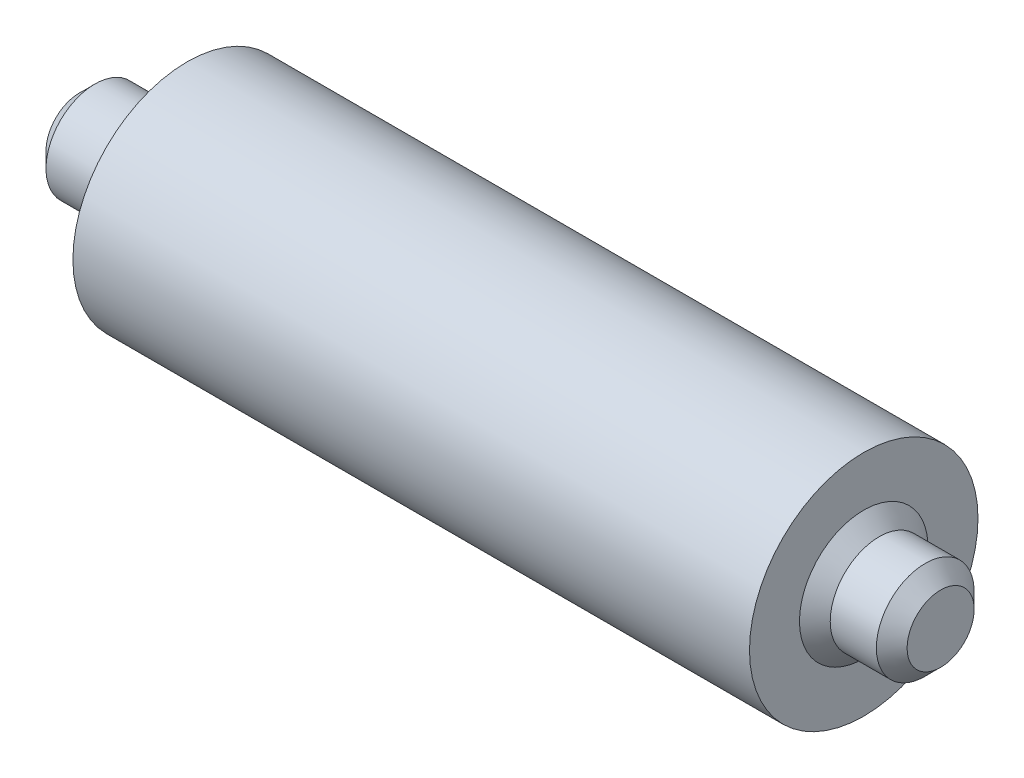
SolidWorks part; units mm, degrees
ref_plane "Front Plane" through (0, 0, 0) normal (0, 0, 1) x (1, 0, 0)
ref_plane "Top Plane" through (0, 0, 0) normal (0, 1, 0) x (1, 0, 0)
ref_plane "Right Plane" through (0, 0, 0) normal (1, 0, 0) x (0, 0, -1)
sketch "Sketch1" plane through (0, 0, 0) normal (0, 0, 1) x (1, 0, 0)
  line L0 (-28.1429, 0) -> (27.8571, 0) construction
  line L1 (-28.1429, 0) -> (-28.1429, 3.18)
  line L2 (-28.1429, 3.18) -> (-21.1429, 3.18)
  line L3 (-21.1429, 3.18) -> (-21.1429, 7.43)
  line L4 (-21.1429, 7.43) -> (22.8571, 7.43)
  line L5 (22.8571, 7.43) -> (22.8571, 3.18)
  line L6 (22.8571, 3.18) -> (27.8571, 3.18)
  line L7 (27.8571, 3.18) -> (27.8571, 0)
  line L8 (-28.1429, 0) -> (27.8571, 0)
  point P1 (-28.1429, 1.59)
  point P4 (-28.1429, 0)
  dimension "D1" = 56
  dimension "D2" = 44
  dimension "D3" = 3.18
  dimension "D4" = 3.18
  dimension "D5" = 4.25
revolve "Revolve1" add sketch "Sketch1" angle 360 about L0
chamfer "Chamfer1" distance 1 angle 45 2 edges at (-28.1429, 0, 3.18) (27.8571, 0, 3.18)
chamfer "Chamfer2" distance 1 angle 45 2 edges at (-21.1429, 0, 3.18) (22.8571, 0, 3.18)
